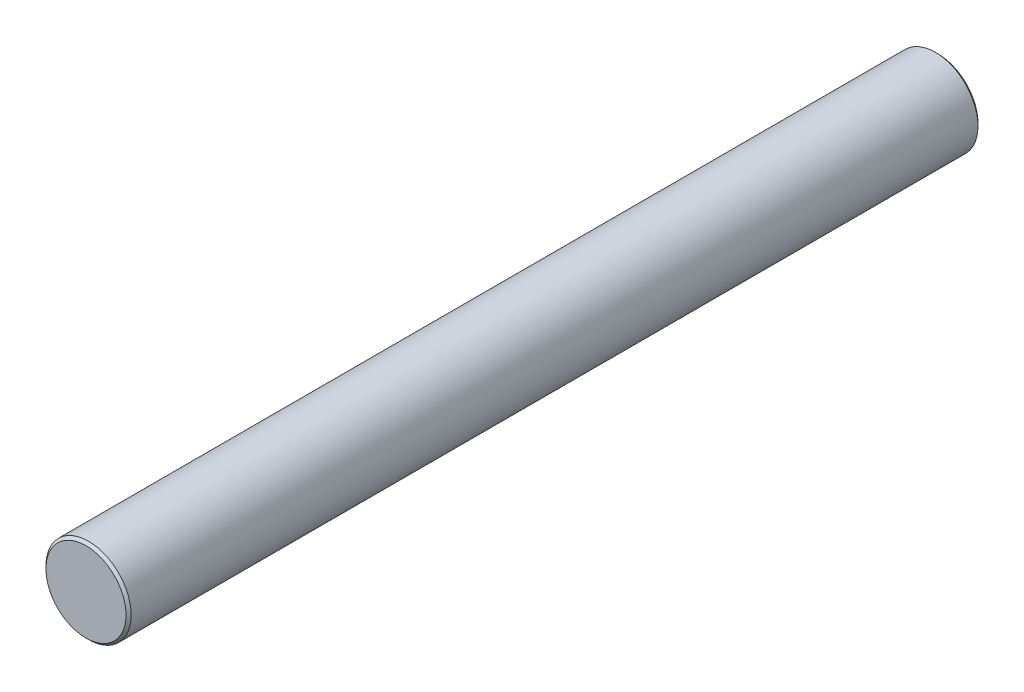
SolidWorks part; units mm, degrees
ref_plane "Front Plane" through (0, 0, 0) normal (0, 0, 1) x (1, 0, 0)
ref_plane "Top Plane" through (0, 0, 0) normal (0, 1, 0) x (1, 0, 0)
ref_plane "Right Plane" through (0, 0, 0) normal (1, 0, 0) x (0, 0, -1)
sketch "Sketch1" plane through (0, 0, 0) normal (0, 0, 1) x (1, 0, 0)
  circle A0 centre (0, 0) radius 5
  dimension "D1" = 10
extrude "Boss-Extrude1" add sketch "Sketch1" along normal mid plane 100
chamfer "Chamfer1" distance 0.3 angle 45 2 edges at (5, 0, -50) (5, 0, 50)
